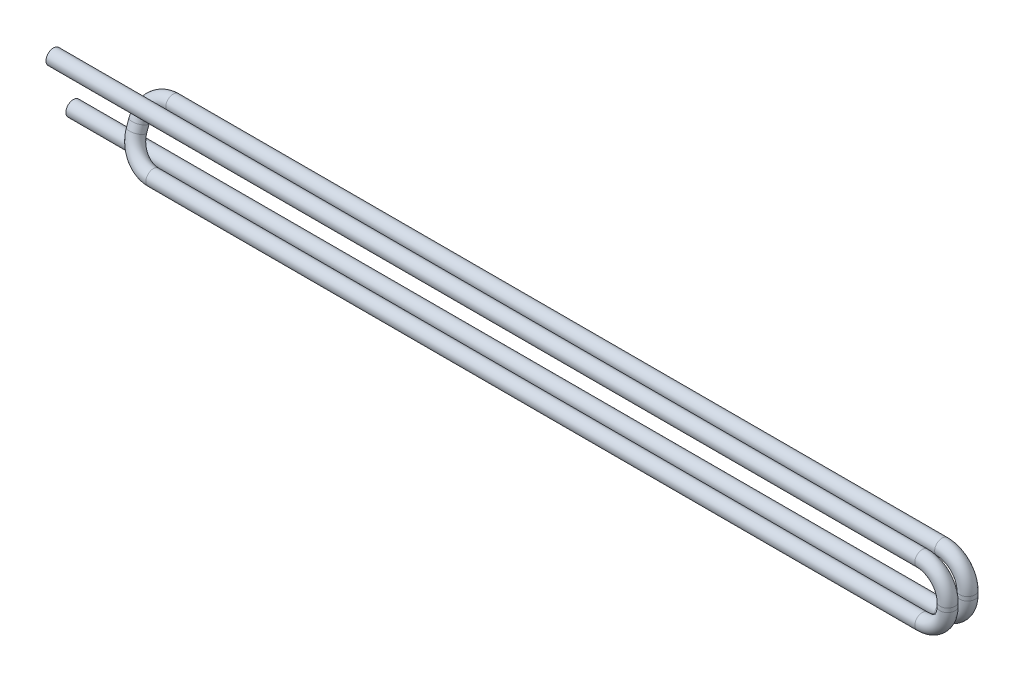
SolidWorks part; units mm, degrees
ref_plane "Front Plane" through (0, 0, 0) normal (0, 0, 1) x (1, 0, 0)
ref_plane "Top Plane" through (0, 0, 0) normal (0, 1, 0) x (1, 0, 0)
ref_plane "Right Plane" through (0, 0, 0) normal (1, 0, 0) x (0, 0, -1)
sketch3d "3DSketch3"
  line L0 (-36, 0, 0) -> (-1.0213, 0, 0)
  line L1 (0, 1.0213, 0) -> (0, 1.1787, 0)
  line L2 (-1.0213, 2.2, 0) -> (-31.9787, 2.2, 0)
  line L3 (-33, 1.2402, 0.349) -> (-33, 0.9598, 0.451)
  line L4 (-31.9787, 0, 0.8) -> (-1.0213, 0, 0.8)
  line L5 (0, 1.0213, 0.8) -> (0, 1.1787, 0.8)
  line L6 (-1.0213, 2.2, 0.8) -> (-36, 2.2, 0.8)
  arc A12 (-31.9787, 2.2, 0) -> (-33, 1.2402, 0.349) centre (-31.9787, 1.2402, 0.349) ccw
  arc A13 (-33, 0.9598, 0.451) -> (-31.9787, 0, 0.8) centre (-31.9787, 0.9598, 0.451) ccw
  arc A14 (-1.0213, 0, 0) -> (0, 1.0213, 0) centre (-1.0213, 1.0213, 0) ccw
  arc A15 (-1.0213, 0, 0.8) -> (0, 1.0213, 0.8) centre (-1.0213, 1.0213, 0.8) ccw
  arc A26 (-1.0213, 2.2, 0) -> (0, 1.1787, 0) centre (-1.0213, 1.1787, 0) ccw
  arc A27 (0, 1.1787, 0.8) -> (-1.0213, 2.2, 0.8) centre (-1.0213, 1.1787, 0.8) ccw
  point P0 (0, 0, 0)
  point P1 (-36, 0, 0)
  point P6 (-33, 2.2, 0)
  point P7 (0, 2.2, 0)
  point P10 (0, 2.2, 0.8)
  point P11 (0, 0, 0.8)
  point P12 (-33, 0, 0.8)
  point P113 (-33, 2.2, 0)
  point P114 (-31.9787, 1.5892, 1.3088)
  point P117 (-33, 0, 0.8)
  point P118 (-31.9787, 1.3088, 1.4108)
  point P121 (0, 0, 0)
  point P122 (-1.0213, 1.0213, 1.0213)
  point P125 (0, 0, 0.8)
  point P126 (-1.0213, 1.0213, 1.8213)
  point P169 (0, 2.2, 0)
  point P170 (-1.0213, 1.1787, -1.0213)
  point P173 (0, 2.2, 0.8)
  point P174 (-1.0213, 1.1787, 1.8213)
ref_plane "Plane1" through (-36, 0, 0) normal (1, 0, 0) x (0, 0, -1)
sketch "Sketch6" plane through (0, 0, 0) normal (0, 0, 1) x (1, 0, 0)
  line L2 (-33.7725, -1.2795) -> (1.1635, -1.2795)
  line L3 (-33.7725, -1.2795) -> (-33.7725, 9.2472)
  line L4 (-33.7725, 9.2472) -> (1.1635, 9.2472)
  line L5 (1.1635, -1.2795) -> (1.1635, 9.2472)
sketch "Sketch5" plane through (-36, 0, 0) normal (1, 0, 0) x (0, 0, -1)
  circle A0 centre (0, 0) radius 0.3
sweep "Sweep4" add profiles "Sketch5" path "3DSketch3"
